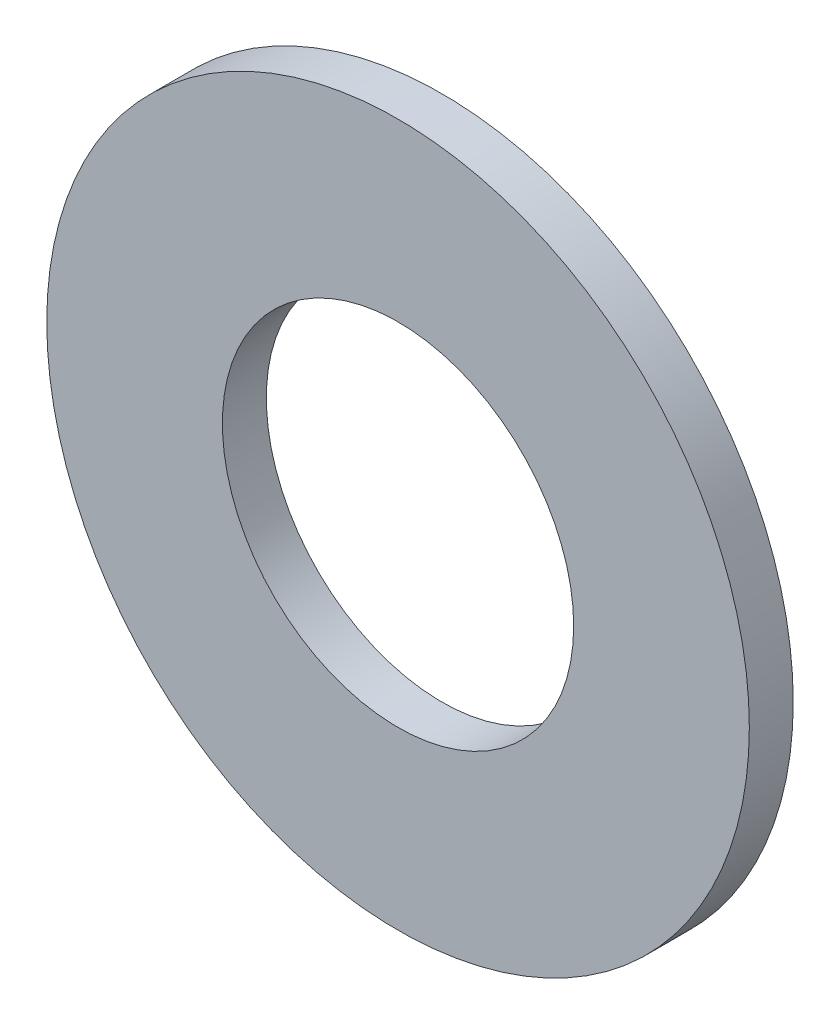
SolidWorks part; units mm, degrees
ref_plane "前视基准面" through (0, 0, 0) normal (0, 0, 1) x (1, 0, 0)
ref_plane "上视基准面" through (0, 0, 0) normal (0, 1, 0) x (1, 0, 0)
ref_plane "右视基准面" through (0, 0, 0) normal (1, 0, 0) x (0, 0, -1)
sketch "草图1" plane through (0, 0, 0) normal (0, 0, 1) x (1, 0, 0)
  circle A0 centre (0, 0) radius 4
  circle A1 centre (0, 0) radius 2
  dimension "D1" = 4
  dimension "D2" = 8
extrude "凸台-拉伸1" add sketch "草图1" along normal blind 0.5
